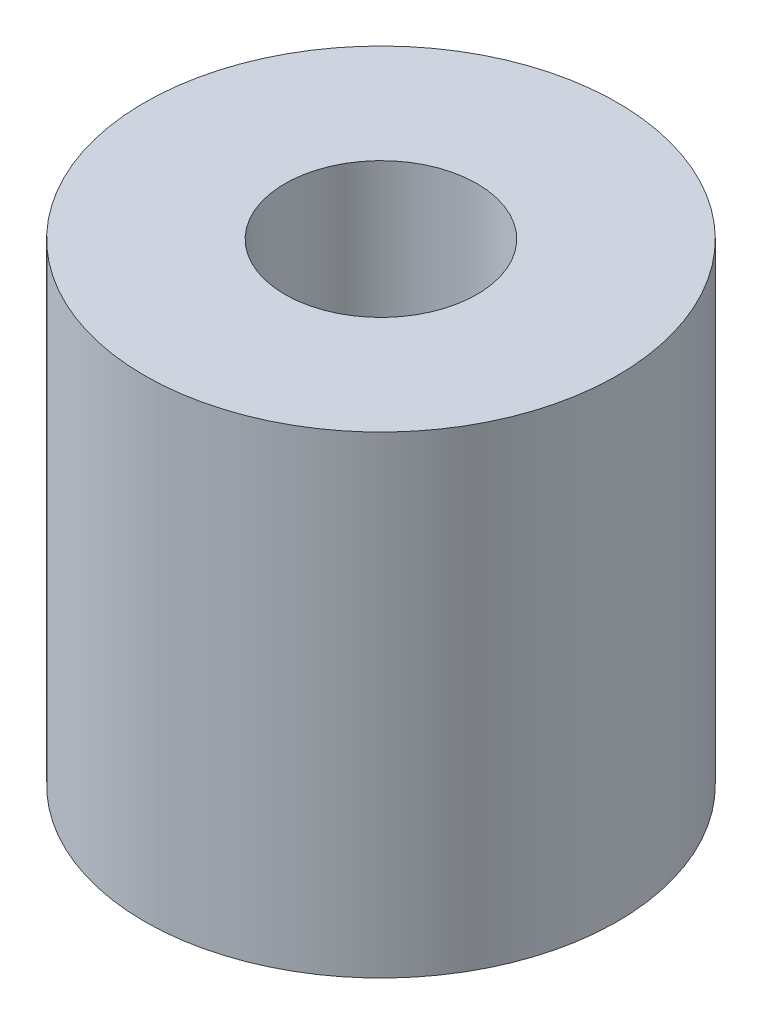
SolidWorks part; units mm, degrees
ref_plane "Front Plane" through (0, 0, 0) normal (0, 0, 1) x (1, 0, 0)
ref_plane "Top Plane" through (0, 0, 0) normal (0, 1, 0) x (1, 0, 0)
ref_plane "Right Plane" through (0, 0, 0) normal (1, 0, 0) x (0, 0, -1)
sketch "Sketch1" plane through (0, 0, 0) normal (0, 1, 0) x (1, 0, 0)
  circle A0 centre (0, 0) radius 4
  circle A1 centre (0, 0) radius 1.625
  dimension "D1" = 8
  dimension "D2" = 3.25
extrude "Boss-Extrude1" add sketch "Sketch1" along normal blind 8
